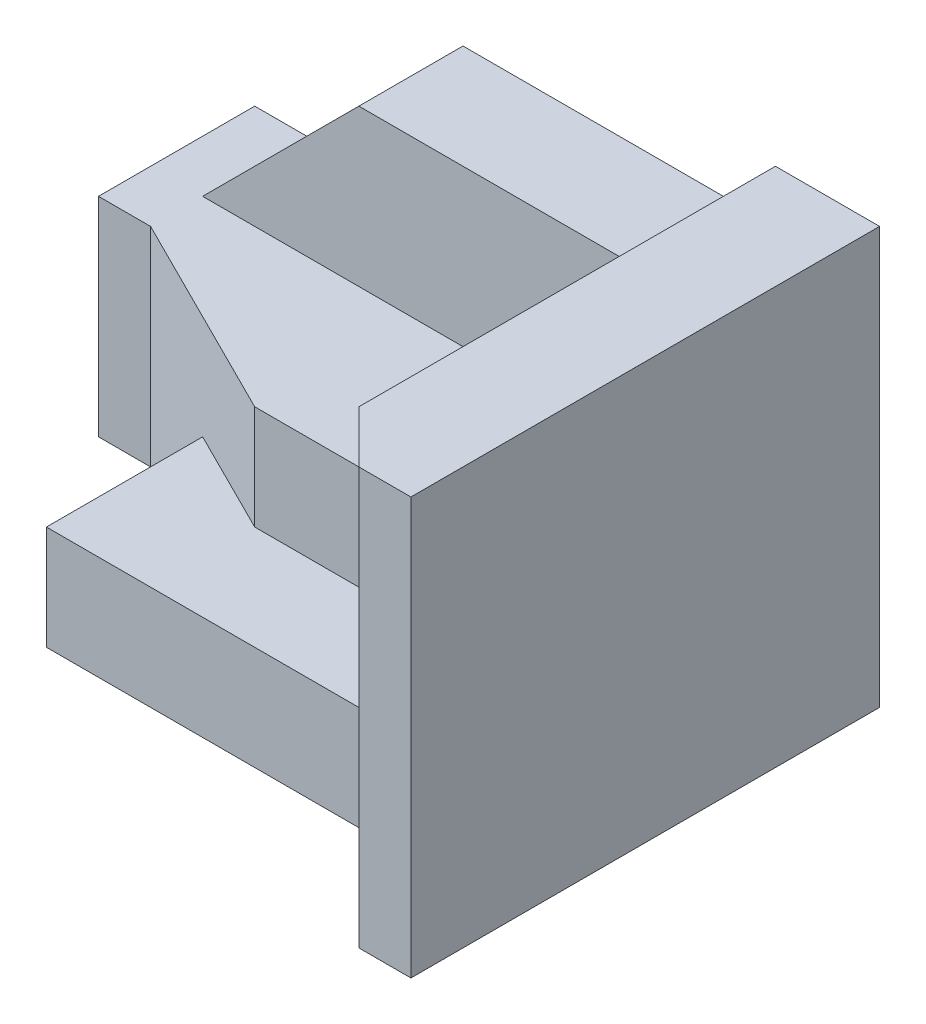
SolidWorks part; units mm, degrees
ref_plane "Front Plane" through (0, 0, 0) normal (0, 0, 1) x (1, 0, 0)
ref_plane "Top Plane" through (0, 0, 0) normal (0, 1, 0) x (1, 0, 0)
ref_plane "Right Plane" through (0, 0, 0) normal (1, 0, 0) x (0, 0, -1)
sketch "Sketch1" plane through (0, 0, 0) normal (0, 0, 1) x (1, 0, 0)
  line L1 (0, 0) -> (120, 0)
  line L2 (0, 0) -> (0, 80)
  line L3 (0, 80) -> (120, 80)
  line L4 (120, 0) -> (120, 80)
  dimension "D1" = 120
  dimension "D2" = 80
extrude "Boss-Extrude1" add sketch "Sketch1" against normal blind 90
sketch "Sketch2" plane through (0, 0, 0) normal (0, 0, 1) x (1, 0, 0)
  line L0 (0, 40) -> (10, 40)
  line L1 (0, 80) -> (0, 0) construction
  line L2 (10, 40) -> (40, 70)
  line L3 (40, 70) -> (100, 70)
  line L4 (100, 70) -> (100, 80)
  line L5 (120, 80) -> (0, 80) construction
  line L6 (100, 80) -> (0, 80)
  line L7 (0, 80) -> (0, 40)
  dimension "D1" = 20
  dimension "D2" = 10
  dimension "D3" = 40
  dimension "D4" = 10
  dimension "D5" = 30
extrude "Cut-Extrude1" cut sketch "Sketch2" against normal blind 90
sketch "Sketch3" plane through (0, 0, 0) normal (0, -1, 0) x (1, 0, 0)
  line L0 (0, -60) -> (10, -60)
  line L1 (0, -90) -> (0, 0) construction
  line L2 (10, -60) -> (30, -50)
  line L3 (30, -50) -> (30, -20)
  line L4 (30, -20) -> (90, -20)
  line L5 (90, -20) -> (110, 0)
  line L6 (0, 0) -> (120, 0) construction
  line L7 (110, 0) -> (0, 0)
  line L8 (0, 0) -> (0, -60)
  dimension "D1" = 30
  dimension "D2" = 10
  dimension "D3" = 10
  dimension "D4" = 20
  dimension "D5" = 30
  dimension "D6" = 60
  dimension "D7" = 10
extrude "Cut-Extrude2" cut sketch "Sketch3" against normal blind 90
ref_plane "Plane1" through (0, 20, 0) normal (0, 1, 0) x (1, 0, 0)
sketch "Sketch4" plane through (0, 20, 0) normal (0, 1, 0) x (1, 0, 0)
  line L0 (30, 20) -> (30, 50)
  line L1 (30, 50) -> (50, 40)
  line L2 (50, 40) -> (70, 40)
  line L3 (70, 40) -> (90, 20)
  line L4 (90, 20) -> (30, 20)
  dimension "D1" = 60
  dimension "D2" = 30
  dimension "D3" = 20
  dimension "D4" = 10
  dimension "D5" = 20
  dimension "D6" = 30
  dimension "D7" = 40
extrude "Cut-Extrude3" cut sketch "Sketch4" along normal blind 90
ref_plane "Plane2" through (0, 40, 0) normal (0, 1, 0) x (1, 0, 0)
sketch "Sketch5" plane through (0, 40, 0) normal (0, 1, 0) x (1, 0, 0)
  line L0 (70, 40) -> (70, 70)
  line L1 (70, 70) -> (10, 70)
  line L2 (10, 90) -> (10, 60) construction
  line L3 (10, 70) -> (10, 60)
  line L4 (10, 60) -> (50, 40)
  line L5 (50, 40) -> (70, 40)
  line L6 (70, 40) -> (50, 40) construction
  dimension "D1" = 20
  dimension "D2" = 30
  dimension "D3" = 0
  dimension "D4" = 0
extrude "Cut-Extrude4" cut sketch "Sketch5" along normal blind 90
sketch "Sketch6" plane through (0, 0, -70) normal (0, 0, 1) x (1, 0, 0)
  line L0 (70, 40) -> (100, 70)
  line L1 (70, 40) -> (70, 70)
  line L2 (70, 70) -> (100, 70)
  line L4 (40, 70) -> (100, 70) construction
  dimension "D1" = 30
extrude "Cut-Extrude5" cut sketch "Sketch6" along normal blind 90
